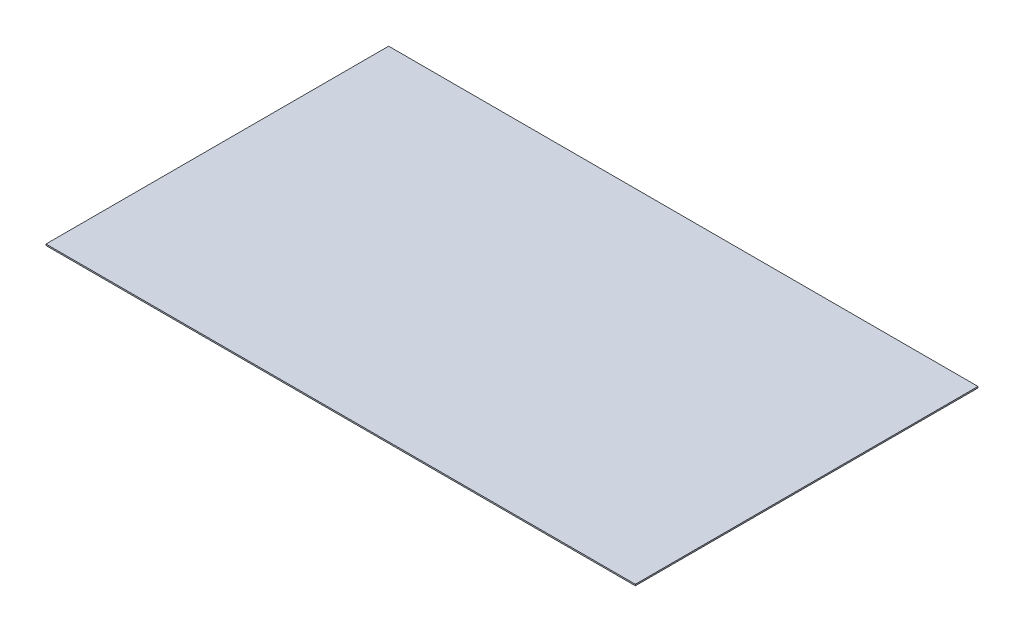
SolidWorks part; units mm, degrees
ref_plane "前视基准面" through (0, 0, 0) normal (0, 0, 1) x (1, 0, 0)
ref_plane "上视基准面" through (0, 0, 0) normal (0, 1, 0) x (1, 0, 0)
ref_plane "右视基准面" through (0, 0, 0) normal (1, 0, 0) x (0, 0, -1)
sketch "草图1" plane through (0, 0, 0) normal (0, 1, 0) x (1, 0, 0)
  line L1 (0, 0) -> (430, 0)
  line L2 (0, 0) -> (0, 250)
  line L3 (0, 250) -> (430, 250)
  line L4 (430, 0) -> (430, 250)
extrude "凸台-拉伸2" add sketch "草图1" along normal blind 1
sketch "草图2" plane through (0, 1, 0) normal (0, 1, 0) x (1, 0, 0)
  circle A0 centre (40, 142) radius 2
  circle A1 centre (130, 142) radius 2
  circle A2 centre (198, 142) radius 2
  circle A3 centre (40, 40) radius 2
  circle A4 centre (114.5, 36.5) radius 2
  circle A5 centre (198, 36.5) radius 2
